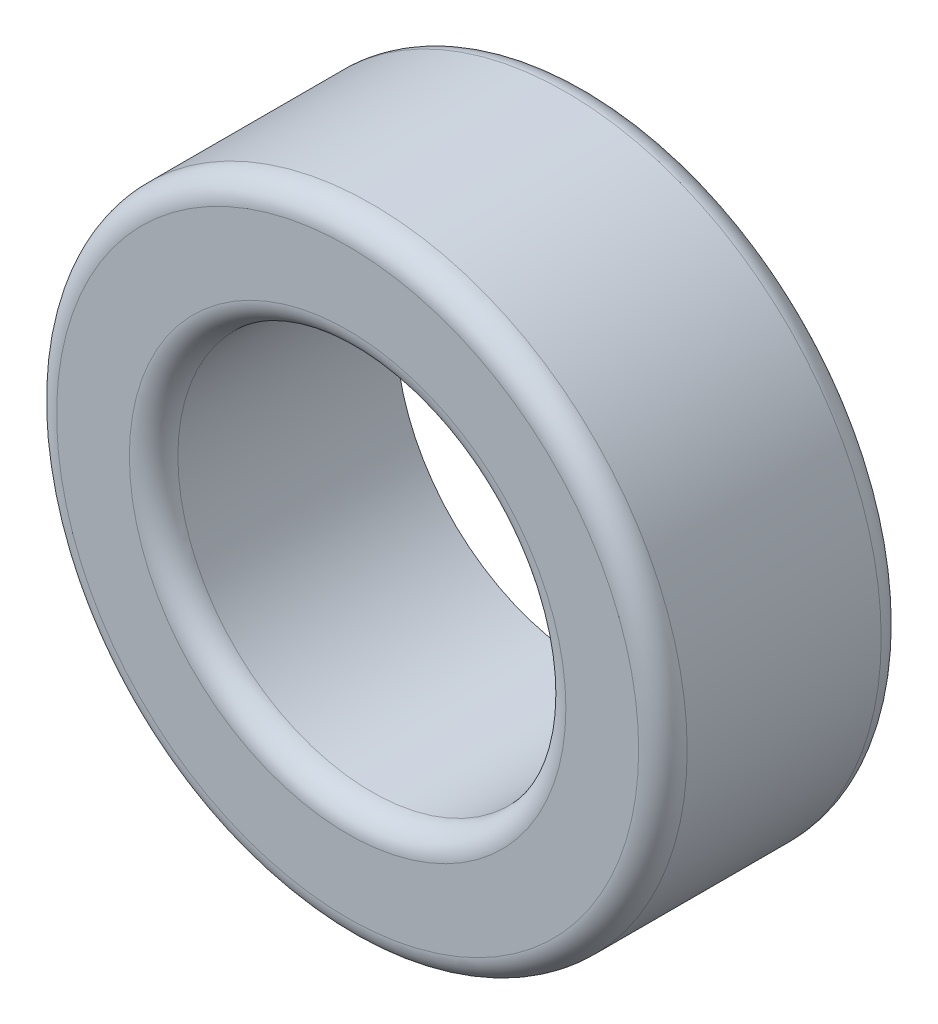
SolidWorks part; units mm, degrees
ref_plane "前视基准面" through (0, 0, 0) normal (0, 0, 1) x (1, 0, 0)
ref_plane "上视基准面" through (0, 0, 0) normal (0, 1, 0) x (1, 0, 0)
ref_plane "右视基准面" through (0, 0, 0) normal (1, 0, 0) x (0, 0, -1)
sketch "草图1" plane through (0, 0, 0) normal (0, 0, 1) x (1, 0, 0)
  circle A0 centre (0, 0) radius 4
  circle A1 centre (0, 0) radius 6.5
  dimension "D1" = 8
  dimension "D2" = 13
extrude "凸台-拉伸1" add sketch "草图1" along normal blind 5
fillet "圆角1" radius 0.5 3 edges at (6.5, 0, 5) (6.5, 0, 0) (4, 0, 5)
